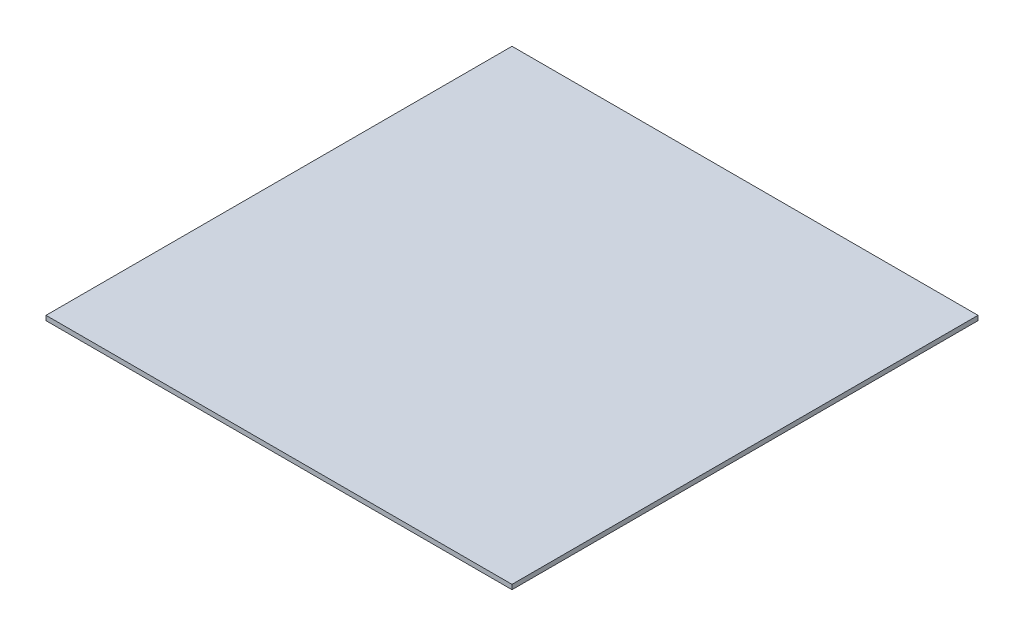
SolidWorks part; units mm, degrees
ref_plane "Front Plane" through (0, 0, 0) normal (0, 0, 1) x (1, 0, 0)
ref_plane "Top Plane" through (0, 0, 0) normal (0, 1, 0) x (1, 0, 0)
ref_plane "Right Plane" through (0, 0, 0) normal (1, 0, 0) x (0, 0, -1)
sketch "Sketch1" plane through (0, 0, 0) normal (0, 1, 0) x (1, 0, 0)
  line L1 (-193.8166, 50.2033) -> (6.1834, 50.2033)
  line L2 (-193.8166, 50.2033) -> (-193.8166, -149.7967)
  line L3 (-193.8166, -149.7967) -> (6.1834, -149.7967)
  line L4 (6.1834, 50.2033) -> (6.1834, -149.7967)
  dimension "D1" = 200
  dimension "D2" = 200
extrude "Boss-Extrude1" add sketch "Sketch1" along normal blind 2
